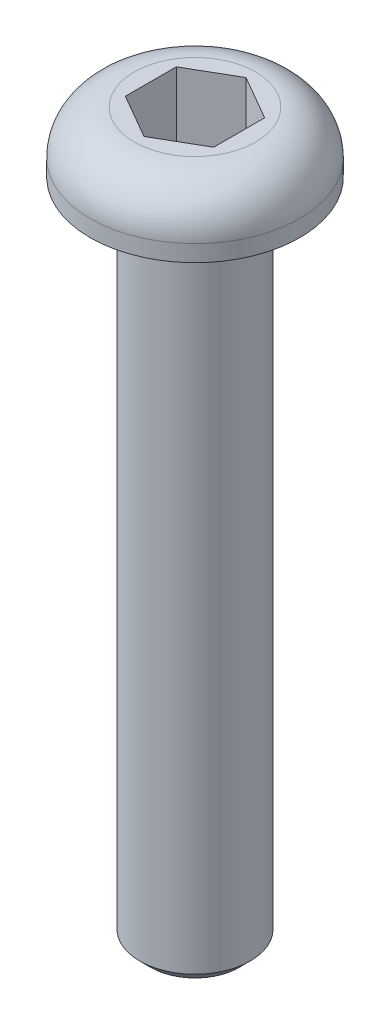
SolidWorks part; units mm, degrees
material "acero"
ref_plane "Alzado" through (0, 0, 0) normal (0, 0, 1) x (1, 0, 0)
ref_plane "Planta" through (0, 0, 0) normal (0, 1, 0) x (1, 0, 0)
ref_plane "Vista lateral" through (0, 0, 0) normal (1, 0, 0) x (0, 0, -1)
sketch "Croquis1" plane through (0, 0, 0) normal (0, 0, 1) x (1, 0, 0)
  line L0 (0, 0) -> (0, -60.9498) construction
  line L1 (0, 0) -> (4.75, 0)
  line L2 (4.75, 0) -> (4.75, -2.75)
  line L3 (4.75, -2.75) -> (2.5, -2.75)
  line L4 (2.5, -2.75) -> (2.5, -32.75)
  line L5 (2.5, -32.75) -> (0, -32.75)
  line L6 (0, -32.75) -> (0, 0)
  dimension "D1" = 30
  dimension "D2" = 2.75
  dimension "D3" = 9.5
  dimension "D4" = 5
revolve "Revolución1" add sketch "Croquis1" angle 360 about L0
sketch "Croquis2" plane through (0, 0, 0) normal (0, 1, 0) x (1, 0, 0)
  line L1 (2, 1.1547) -> (0, 2.3094)
  line L2 (0, 2.3094) -> (-2, 1.1547)
  line L3 (-2, 1.1547) -> (-2, -1.1547)
  line L4 (-2, -1.1547) -> (0, -2.3094)
  line L5 (0, -2.3094) -> (2, -1.1547)
  line L6 (2, -1.1547) -> (2, 1.1547)
  circle A0 centre (0, 0) radius 2 construction
  dimension "D1" = 4
extrude "Cortar-Extruir1" cut sketch "Croquis2" against normal blind 3.5
chamfer "Chaflán1" distance 0.5 angle 45 1 edges at (0, -32.75, 2.5)
fillet "Redondeo1" radius 2 1 edges at (0, 0, 4.75)
